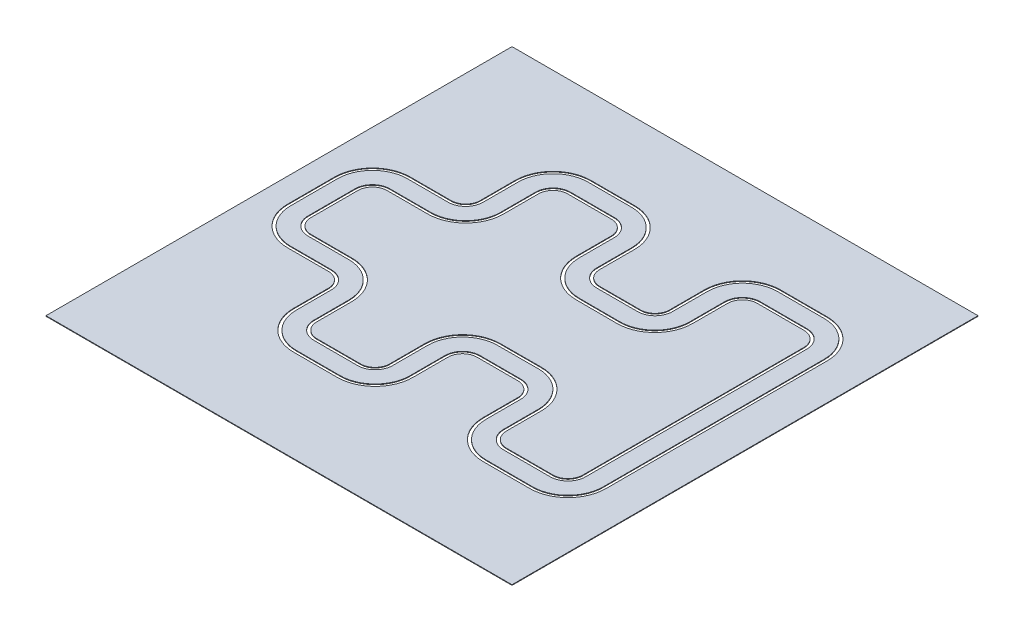
SolidWorks part; units mm, degrees
ref_plane "Front Plane" through (0, 0, 0) normal (0, 0, 1) x (1, 0, 0)
ref_plane "Top Plane" through (0, 0, 0) normal (0, 1, 0) x (1, 0, 0)
ref_plane "Right Plane" through (0, 0, 0) normal (1, 0, 0) x (0, 0, -1)
sketch "Sketch1" plane through (0, 0, 0) normal (0, 1, 0) x (1, 0, 0)
  line L34 (-1771.8006, -1038.9171) -> (-1771.8006, -1638.9171)
  line L39 (-1821.8006, -1638.9171) -> (-1821.8006, -1038.9171)
  line L40 (-2121.8006, -1638.9171) -> (-2121.8006, -1038.9171)
  line L44 (-2171.8006, -1038.9171) -> (-2171.8006, -1638.9171)
  line L64 (-1521.8006, -1888.9171) -> (-770.5984, -1888.9171)
  line L66 (-1521.8006, -1938.9171) -> (-770.5984, -1938.9171)
  line L68 (-1521.8006, -2238.9171) -> (-770.5984, -2238.9171)
  line L69 (-1521.8006, -2288.9171) -> (-770.5984, -2288.9171)
  line L82 (-520.5984, -1638.9171) -> (-520.5984, -1037.2411)
  line L83 (-4187.7678, 4128.3252) -> (-4187.7678, -3871.6748)
  line L84 (3812.2322, 4128.3252) -> (3812.2322, -3871.6748)
  line L89 (-470.5984, -1638.9171) -> (-470.5984, -1037.2888)
  line L90 (-170.5984, -1638.9171) -> (-170.5984, -1038.9169)
  line L91 (-120.5984, -1638.9171) -> (-120.5984, -1038.9256)
  line L92 (1079.7634, -1638.958) -> (1079.7634, -1038.9495)
  line L93 (1129.7573, -1638.9164) -> (1129.7573, -1038.9166)
  line L94 (1429.6382, -1633.7532) -> (1429.6382, -1035.3859)
  line L95 (1479.5992, -1633.7532) -> (1479.5992, -1035.4334)
  line L96 (129.4102, -788.9256) -> (829.772, -788.9495)
  line L102 (129.4015, -738.9169) -> (829.7571, -738.9166)
  line L103 (127.7711, -437.291) -> (828.0077, -435.3881)
  line L105 (127.7235, -387.2433) -> (827.9211, -385.4356)
  line L106 (-2421.8006, -788.9171) -> (-3121.8006, -788.9171)
  line L107 (-2421.8006, -738.9171) -> (-3121.8006, -738.9171)
  line L108 (-2421.8006, -438.9171) -> (-3121.8006, -438.9171)
  line L109 (-2421.8006, -388.9171) -> (-3121.8006, -388.9171)
  line L110 (2789.9845, 1563.2807) -> (2789.9845, -1035.4334)
  line L111 (2839.9456, 1563.2332) -> (2839.9456, -1035.3859)
  line L112 (3139.8265, 1566.7639) -> (3139.8265, -1038.9166)
  line L113 (3189.8203, 1566.7968) -> (3189.8203, -1038.9495)
  line L114 (-4187.7678, 4128.3252) -> (3812.2322, 4128.3252)
  line L126 (-3771.8006, -138.9171) -> (-3771.8006, 666.7643)
  line L127 (-3721.8006, -138.9171) -> (-3721.8006, 666.7643)
  line L128 (-3421.8006, -138.9171) -> (-3421.8006, 666.7643)
  line L129 (-3371.8006, -138.9171) -> (-3371.8006, 666.7643)
  line L130 (1734.7919, -1888.9458) -> (2534.7919, -1888.9458)
  line L132 (1734.7919, -2238.8098) -> (2534.7919, -2238.8098)
  line L133 (1734.7919, -2288.8023) -> (2534.7919, -2288.8023)
  line L135 (1734.8139, 2466.7542) -> (2534.7919, 2466.7542)
  line L136 (1734.7919, -1938.9069) -> (2534.7698, -1938.9069)
  line L149 (2789.9845, -1633.7532) -> (2789.9845, -1035.4334)
  line L150 (2839.9456, -1633.7532) -> (2839.9456, -1035.3859)
  line L151 (3139.8265, -1638.9164) -> (3139.8265, -1038.9166)
  line L152 (3189.8203, -1638.958) -> (3189.8203, -1038.9495)
  line L175 (3189.8203, 2166.8053) -> (3189.8203, 1566.7968)
  line L176 (3139.8265, 2166.7637) -> (3139.8265, 1566.7639)
  line L177 (2839.9456, 2161.6005) -> (2839.9456, 1563.2332)
  line L178 (2789.9845, 2161.6005) -> (2789.9845, 1563.2807)
  line L187 (1734.7919, 2816.6496) -> (2534.7919, 2816.6496)
  line L189 (1734.7919, 2766.6571) -> (2534.7919, 2766.6571)
  line L190 (1734.7919, 2416.7931) -> (2534.7919, 2416.7931)
  line L191 (-2421.8006, 916.7643) -> (-3121.8006, 916.7643)
  line L192 (-2421.8006, 966.7643) -> (-3121.8006, 966.7643)
  line L193 (-2421.8006, 1266.7643) -> (-3121.8006, 1266.7643)
  line L194 (-2421.8006, 1316.7643) -> (-3121.8006, 1316.7643)
  line L195 (127.7235, 915.0906) -> (827.9211, 913.2829)
  line L196 (127.7711, 965.1383) -> (828.0077, 963.2354)
  line L197 (129.4015, 1266.7642) -> (829.7571, 1266.7639)
  line L198 (129.4102, 1316.7729) -> (829.772, 1316.7968)
  line L199 (1479.5992, 2161.6005) -> (1479.5992, 1563.2807)
  line L200 (1429.6382, 2161.6005) -> (1429.6382, 1563.2332)
  line L201 (1129.7573, 2166.7637) -> (1129.7573, 1566.7639)
  line L202 (1079.7634, 2166.8053) -> (1079.7634, 1566.7968)
  line L203 (-120.5984, 2166.7643) -> (-120.5984, 1566.7729)
  line L204 (-170.5984, 2166.7643) -> (-170.5984, 1566.7642)
  line L205 (-470.5984, 2166.7643) -> (-470.5984, 1565.1361)
  line L206 (-520.5984, 2166.7643) -> (-520.5984, 1565.0884)
  line L207 (-1521.8006, 2816.7643) -> (-770.5984, 2816.7643)
  line L208 (-1521.8006, 2766.7643) -> (-770.5984, 2766.7643)
  line L209 (-1521.8006, 2466.7643) -> (-770.5984, 2466.7643)
  line L210 (-1521.8006, 2416.7643) -> (-770.5984, 2416.7643)
  line L211 (-2171.8006, 1566.7643) -> (-2171.8006, 2166.7643)
  line L212 (-2121.8006, 2166.7643) -> (-2121.8006, 1566.7643)
  line L213 (-1821.8006, 2166.7643) -> (-1821.8006, 1566.7643)
  line L214 (-1771.8006, 1566.7643) -> (-1771.8006, 2166.7643)
  line L216 (-4187.7678, -3871.6748) -> (3812.2322, -3871.6748)
  arc A24 (-1521.8006, -1938.9171) -> (-1821.8006, -1638.9171) centre (-1521.8006, -1638.9171) cw
  arc A25 (-1521.8006, -1888.9171) -> (-1771.8006, -1638.9171) centre (-1521.8006, -1638.9171) cw
  arc A26 (-770.5984, -1888.9171) -> (-520.5984, -1638.9171) centre (-770.5984, -1638.9171) ccw
  arc A27 (-770.5984, -1938.9171) -> (-470.5984, -1638.9171) centre (-770.5984, -1638.9171) ccw
  arc A28 (-1521.8006, -2238.9171) -> (-2121.8006, -1638.9171) centre (-1521.8006, -1638.9171) cw
  arc A29 (-770.5984, -2238.9171) -> (-170.5984, -1638.9171) centre (-770.5984, -1638.9171) ccw
  arc A30 (-770.5984, -2288.9171) -> (-120.5984, -1638.9171) centre (-770.5984, -1638.9171) ccw
  arc A31 (-1521.8006, -2288.9171) -> (-2171.8006, -1638.9171) centre (-1521.8006, -1638.9171) cw
  arc A33 (1734.7919, -1888.9458) -> (1479.5992, -1633.7532) centre (1734.7919, -1633.7532) cw
  arc A36 (1734.7919, -1938.9069) -> (1429.6382, -1633.7532) centre (1734.7919, -1633.7532) cw
  arc A39 (1734.7919, -2238.8098) -> (1129.7573, -1638.9164) centre (1734.7919, -1633.7532) cw
  arc A42 (1734.7919, -2288.8023) -> (1079.7634, -1638.958) centre (1734.7919, -1633.7532) cw
  arc A52 (1079.7634, -1038.9495) -> (829.772, -788.9495) centre (829.7634, -1038.9495) ccw
  arc A53 (129.4102, -788.9256) -> (-120.5984, -1038.9256) centre (129.4016, -1038.9256) ccw
  arc A54 (829.7571, -738.9166) -> (1129.7573, -1038.9166) centre (829.7573, -1038.9166) cw
  arc A55 (129.4015, -738.9169) -> (-170.5984, -1038.9169) centre (129.4016, -1038.9169) ccw
  arc A56 (828.0077, -435.3881) -> (1429.6382, -1035.3859) centre (829.6382, -1035.3859) cw
  arc A57 (-470.5984, -1037.2888) -> (127.7711, -437.291) centre (129.4016, -1037.2888) cw
  arc A58 (127.7235, -387.2433) -> (-520.5984, -1037.2411) centre (129.4016, -1037.2411) ccw
  arc A59 (1479.5992, -1035.4334) -> (827.9211, -385.4356) centre (829.5992, -1035.4334) ccw
  arc A60 (-2421.8006, -788.9171) -> (-2171.8006, -1038.9171) centre (-2421.8006, -1038.9171) cw
  arc A61 (-2121.8006, -1038.9171) -> (-2421.8006, -738.9171) centre (-2421.8006, -1038.9171) ccw
  arc A62 (-1821.8006, -1038.9171) -> (-2421.8006, -438.9171) centre (-2421.8006, -1038.9171) ccw
  arc A63 (-1771.8006, -1038.9171) -> (-2421.8006, -388.9171) centre (-2421.8006, -1038.9171) ccw
  arc A64 (-3771.8006, -138.9171) -> (-3121.8006, -788.9171) centre (-3121.8006, -138.9171) ccw
  arc A65 (-3721.8006, -138.9171) -> (-3121.8006, -738.9171) centre (-3121.8006, -138.9171) ccw
  arc A66 (-3121.8006, -438.9171) -> (-3421.8006, -138.9171) centre (-3121.8006, -138.9171) cw
  arc A67 (-3371.8006, -138.9171) -> (-3121.8006, -388.9171) centre (-3121.8006, -138.9171) ccw
  arc A96 (2534.7919, -2288.8023) -> (3189.8203, -1638.958) centre (2534.7919, -1633.7532) ccw
  arc A97 (2534.7919, -2238.8098) -> (3139.8265, -1638.9164) centre (2534.7919, -1633.7532) ccw
  arc A98 (2534.7698, -1938.9069) -> (2839.9456, -1633.7532) centre (2534.7919, -1633.7532) ccw
  arc A99 (2534.7919, -1888.9458) -> (2789.9845, -1633.7532) centre (2534.7919, -1633.7532) ccw
  arc A116 (2534.7919, 2416.7931) -> (2789.9845, 2161.6005) centre (2534.7919, 2161.6005) cw
  arc A117 (2534.7919, 2466.7542) -> (2839.9456, 2161.6005) centre (2534.7919, 2161.6005) cw
  arc A118 (2534.7919, 2766.6571) -> (3139.8265, 2166.7637) centre (2534.7919, 2161.6005) cw
  arc A119 (2534.7919, 2816.6496) -> (3189.8203, 2166.8053) centre (2534.7919, 2161.6005) cw
  arc A136 (-3371.8006, 666.7643) -> (-3121.8006, 916.7643) centre (-3121.8006, 666.7643) cw
  arc A137 (-3121.8006, 966.7643) -> (-3421.8006, 666.7643) centre (-3121.8006, 666.7643) ccw
  arc A138 (-3721.8006, 666.7643) -> (-3121.8006, 1266.7643) centre (-3121.8006, 666.7643) cw
  arc A139 (-3771.8006, 666.7643) -> (-3121.8006, 1316.7643) centre (-3121.8006, 666.7643) cw
  arc A140 (-1771.8006, 1566.7643) -> (-2421.8006, 916.7643) centre (-2421.8006, 1566.7643) cw
  arc A141 (-1821.8006, 1566.7643) -> (-2421.8006, 966.7643) centre (-2421.8006, 1566.7643) cw
  arc A142 (-2121.8006, 1566.7643) -> (-2421.8006, 1266.7643) centre (-2421.8006, 1566.7643) cw
  arc A143 (-2421.8006, 1316.7643) -> (-2171.8006, 1566.7643) centre (-2421.8006, 1566.7643) ccw
  arc A144 (1479.5992, 1563.2807) -> (827.9211, 913.2829) centre (829.5992, 1563.2807) cw
  arc A145 (127.7235, 915.0906) -> (-520.5984, 1565.0884) centre (129.4016, 1565.0884) cw
  arc A146 (-470.5984, 1565.1361) -> (127.7711, 965.1383) centre (129.4016, 1565.1361) ccw
  arc A147 (828.0077, 963.2354) -> (1429.6382, 1563.2332) centre (829.6382, 1563.2332) ccw
  arc A148 (129.4015, 1266.7642) -> (-170.5984, 1566.7642) centre (129.4016, 1566.7642) cw
  arc A149 (829.7571, 1266.7639) -> (1129.7573, 1566.7639) centre (829.7573, 1566.7639) ccw
  arc A150 (129.4102, 1316.7729) -> (-120.5984, 1566.7729) centre (129.4016, 1566.7729) cw
  arc A151 (1079.7634, 1566.7968) -> (829.772, 1316.7968) centre (829.7634, 1566.7968) cw
  arc A152 (1734.7919, 2816.6496) -> (1079.7634, 2166.8053) centre (1734.7919, 2161.6005) ccw
  arc A153 (1734.7919, 2766.6571) -> (1129.7573, 2166.7637) centre (1734.7919, 2161.6005) ccw
  arc A154 (1734.8139, 2466.7542) -> (1429.6382, 2161.6005) centre (1734.7919, 2161.6005) ccw
  arc A155 (1734.7919, 2416.7931) -> (1479.5992, 2161.6005) centre (1734.7919, 2161.6005) ccw
  arc A156 (-1521.8006, 2816.7643) -> (-2171.8006, 2166.7643) centre (-1521.8006, 2166.7643) ccw
  arc A157 (-770.5984, 2816.7643) -> (-120.5984, 2166.7643) centre (-770.5984, 2166.7643) cw
  arc A158 (-770.5984, 2766.7643) -> (-170.5984, 2166.7643) centre (-770.5984, 2166.7643) cw
  arc A159 (-1521.8006, 2766.7643) -> (-2121.8006, 2166.7643) centre (-1521.8006, 2166.7643) ccw
  arc A160 (-770.5984, 2466.7643) -> (-470.5984, 2166.7643) centre (-770.5984, 2166.7643) cw
  arc A161 (-770.5984, 2416.7643) -> (-520.5984, 2166.7643) centre (-770.5984, 2166.7643) cw
  arc A162 (-1521.8006, 2416.7643) -> (-1771.8006, 2166.7643) centre (-1521.8006, 2166.7643) ccw
  arc A163 (-1521.8006, 2466.7643) -> (-1821.8006, 2166.7643) centre (-1521.8006, 2166.7643) ccw
  point P125 (-3721.8006, 263.9236)
  point P127 (-3421.8006, 263.9236)
  point P344 (-3371.8006, 263.9236)
  dimension "D8" = 300
  dimension "D7" = 250
  dimension "D1" = 8000
  dimension "D2" = 8000
extrude "Boss-Extrude1" add sketch "Sketch1" along normal blind 10 contours L83 L216 L84 L114 L207 A157 L203 A150 L198 A151 L202 A152 L187 A119 L175 L113 L152 A96 L133 A42 L92 A52 L96 A53 L91 A30 L69 A31 L44 A60 L106 A64 L126 A139 L194 A143 L211 A156 | L208 A159 L212 A142 L193 A138 L127 A65 L107 A61 L40 A28 L68 A29 L90 A55 L102 A54 L93 A39 L132 A97 L151 L112 L176 A118 L189 A153 L201 A149 L197 A148 L204 A158 A163 L209 A160 L205 A146 L196 A147 L200 A154 L135 A117 L177 L111 L150 A98 L136 | L210 A162 L214 A140 L191 A136 L129 A67 L109 A63 L34 A25 L64 A26 L82 A58 L105 A59 L95 A33 L130 A99 L149 L110 L178 A116 L190 A155 L199 A144 L195 A145 L206 A161
